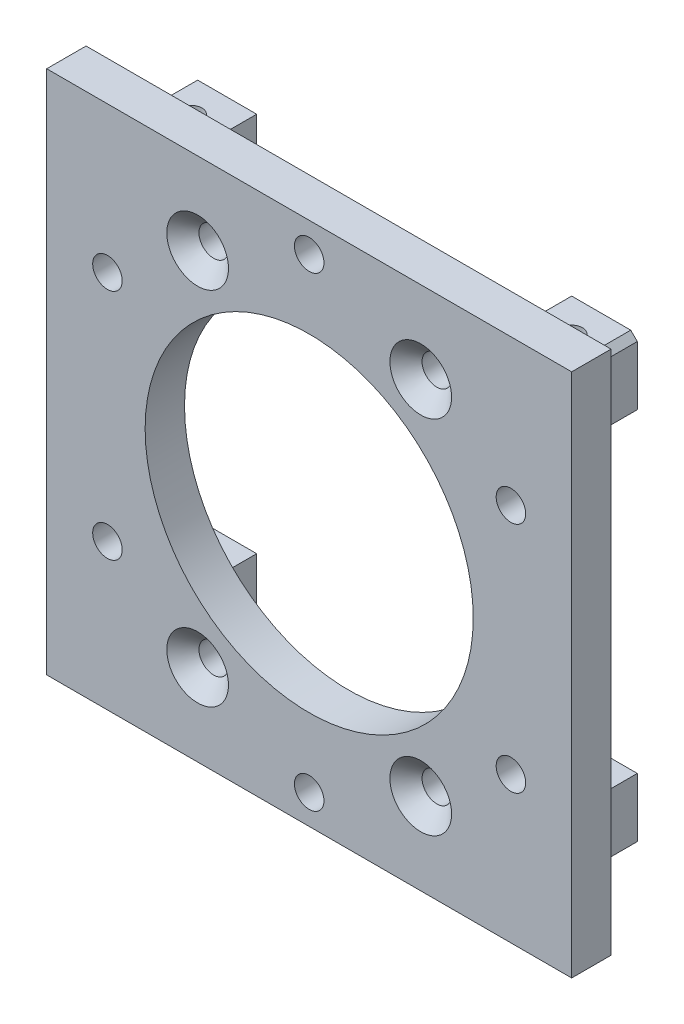
SolidWorks part; units mm, degrees
material "5052-O"
ref_plane "정면" through (0, 0, 0) normal (0, 0, 1) x (1, 0, 0)
ref_plane "윗면" through (0, 0, 0) normal (0, 1, 0) x (1, 0, 0)
ref_plane "우측면" through (0, 0, 0) normal (1, 0, 0) x (0, 0, -1)
sketch "스케치1" plane through (0, 0, 0) normal (0, 0, 1) x (1, 0, 0)
  line L1 (-40, 40) -> (40, 40)
  line L2 (-40, 40) -> (-40, -40)
  line L3 (-40, -40) -> (40, -40)
  line L4 (40, 40) -> (40, -40)
  line L5 (-40, 40) -> (40, -40) construction
  line L6 (-40, -40) -> (40, 40) construction
  circle A0 centre (0, 0) radius 25
  point P0 (0, 0)
  dimension "D3" = 50
  dimension "D1" = 80
  dimension "D2" = 80
extrude "보스-돌출1" add sketch "스케치1" along normal blind 6
sketch "스케치11" plane through (0, 0, 0) normal (0, 0, -1) x (-1, 0, 0)
  line L0 (40, 40) -> (40, -40) construction
  line L1 (34, 34) -> (24, 34)
  line L2 (34, 34) -> (34, 24)
  line L3 (34, 24) -> (24, 24)
  line L4 (24, 34) -> (24, 24)
  line L5 (34, 34) -> (24, 24) construction
  line L6 (34, 24) -> (24, 34) construction
  line L7 (-40, 40) -> (40, 40) construction
  point P0 (29, 29)
  dimension "D1" = 10
  dimension "D2" = 10
  dimension "D3" = 6
  dimension "D4" = 6
extrude "보스-돌출3" add sketch "스케치11" along normal blind 10
hole_wizard "M4 육각 소켓 접시 머리 캡 나사용 카운터싱크1" positions "스케치5" profile "스케치6" countersink size "M4" standard "ISO" end condition through all
sketch "스케치5" plane through (0, 0, 0) normal (0, 0, -1) x (-1, 0, 0)
  line L1 (30.7439, -17.75) -> (30.7439, 17.75)
  line L2 (30.7439, 17.75) -> (0, 35.5)
  line L3 (0, 35.5) -> (-30.7439, 17.75)
  line L4 (-30.7439, 17.75) -> (-30.7439, -17.75)
  line L5 (-30.7439, -17.75) -> (0, -35.5)
  line L6 (0, -35.5) -> (30.7439, -17.75)
  line L10 (0, 35.5) -> (0, -35.5)
  line L12 (0, 0) -> (20.1285, 0)
  circle A0 centre (0, 0) radius 35.5 construction
  point P3 (30.7439, -17.75)
  point P4 (30.7439, 17.75)
  point P5 (0, 35.5)
  point P6 (-30.7439, 17.75)
  point P7 (-30.7439, -17.75)
  point P8 (0, -35.5)
  dimension "D1" = 71
  dimension "D2" = 90
sketch "스케치6" plane through (0, -35.5, 0) normal (1, 0, 0) x (0, 1, 0)
  line L0 (0, 0) -> (0, 6)
  line L1 (0, 6) -> (2.25, 6)
  line L2 (2.25, 6) -> (2.25, 2.23)
  line L3 (2.25, 2.23) -> (4.48, 0)
  line L5 (4.48, 0) -> (0, 0)
  line L6 (-2.25, 2.23) -> (-4.48, 0) construction
  line L11 (0, -6.35) -> (0, 107.95) construction
  dimension "관통 구멍 지름" = 4.5
  dimension "관통 구멍 깊이" = 6
  dimension "표면 카운터싱크 지름" = 8.96
  dimension "표면 카운터싱크 각도" = 90
hole_wizard "M4 나사 구멍2" positions "스케치12" profile "스케치13" tap size "M4" standard "ISO" end condition up to next
sketch "스케치12" plane through (0, 34, 0) normal (0, 1, 0) x (1, 0, 0)
  line L0 (-34, 10) -> (-34, 0) construction
  line L1 (-34, 10) -> (-24, 10) construction
  point P0 (-29, 5)
  point P6 (-34, 5)
  point P9 (-29, 10)
sketch "스케치13" plane through (-29, 34, -5) normal (1, 0, 0) x (0, 0, 1)
  line L0 (0, 0) -> (0, 68)
  line L1 (0, 68) -> (1.65, 68)
  line L2 (1.65, 68) -> (1.65, 0)
  line L5 (1.65, 0) -> (0, 0)
  line L11 (0, -6.35) -> (0, 107.95) construction
  dimension "관통 탭 드릴 지름" = 3.3
  dimension "관통 탭 드릴 깊이" = 68
cosmetic thread "구멍 나사산5"
mirror "대칭 복사1" about plane through (0, 0, 0) normal (1, 0, 0) of "M4 나사 구멍2", "보스-돌출3"
cosmetic thread "구멍 나사산8"
mirror "대칭 복사2" about plane through (0, 0, 0) normal (0, 1, 0) of "대칭 복사1", "보스-돌출3", "M4 나사 구멍2"
cosmetic thread "구멍 나사산9"
cosmetic thread "구멍 나사산10"
hole_wizard "M4 접시 머리 나사용 카운터싱크1" positions "스케치14" profile "스케치15" countersink size "M4" standard "ISO" end condition through all
sketch "스케치14" plane through (0, 0, 6) normal (0, 0, 1) x (1, 0, 0)
  line L1 (-17, 27.5) -> (17, 27.5)
  line L2 (-17, 27.5) -> (-17, -27.5)
  line L3 (-17, -27.5) -> (17, -27.5)
  line L4 (17, 27.5) -> (17, -27.5)
  line L5 (-17, 27.5) -> (17, -27.5) construction
  line L6 (-17, -27.5) -> (17, 27.5) construction
  circle A0 centre (0, 0) radius 25 construction
  circle A1 centre (0, 0) radius 25
  point P6 (17, -27.5)
  point P45 (-17, 27.5)
  point P46 (-17, -27.5)
  point P47 (17, 27.5)
  dimension "D1" = 55
  dimension "D2" = 34
sketch "스케치15" plane through (17, 27.5, 6) normal (1, 0, 0) x (0, -1, 0)
  line L0 (0, 0) -> (0, 16)
  line L1 (0, 16) -> (2.25, 16)
  line L2 (2.25, 16) -> (2.25, 2.45)
  line L3 (2.25, 2.45) -> (4.7, 0)
  line L5 (4.7, 0) -> (0, 0)
  line L6 (-2.25, 2.45) -> (-4.7, 0) construction
  line L11 (0, -6.35) -> (0, 107.95) construction
  dimension "관통 구멍 지름" = 4.5
  dimension "관통 구멍 깊이" = 16
  dimension "표면 카운터싱크 지름" = 9.4
  dimension "표면 카운터싱크 각도" = 90
chamfer "모따기1" distance 1 angle 45 4 edges at (34, 34, -5) (34, -34, -5) (-34, -34, -5) (-34, 34, -5)
equation "\"D2@스케치1\"=\"D1@스케치1\""
equation "\"D2@스케치11\"=\"D1@스케치11\""
equation "\"D4@스케치11\"=\"D3@스케치11\""
